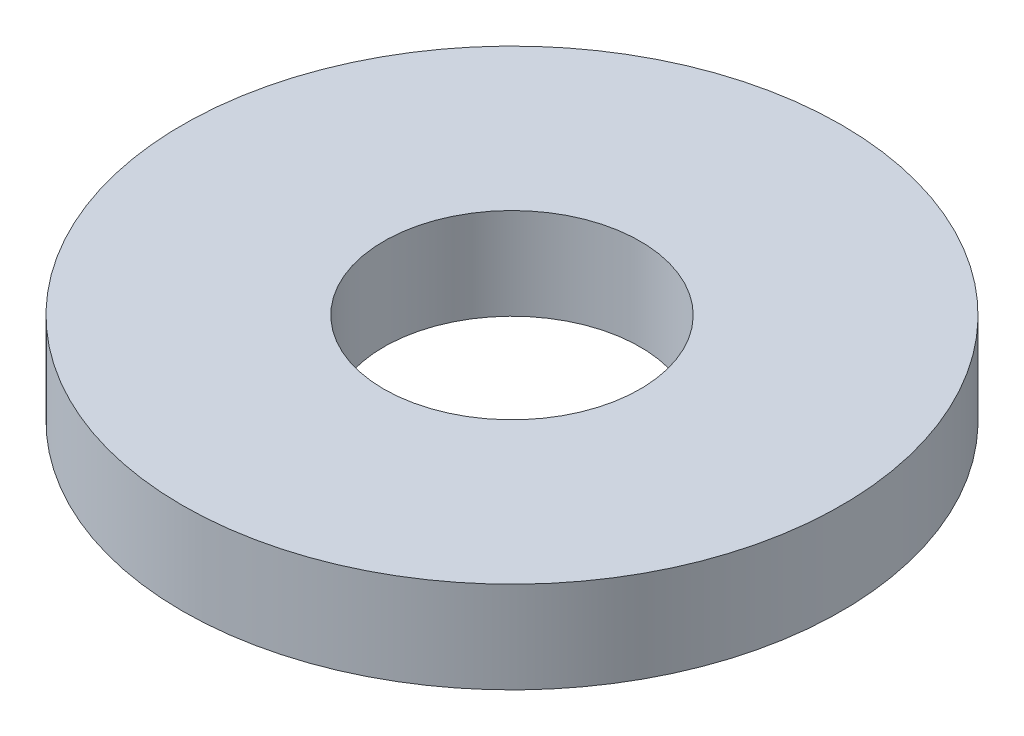
SolidWorks part; units mm, degrees
ref_plane "Front Plane" through (0, 0, 0) normal (0, 0, 1) x (1, 0, 0)
ref_plane "Top Plane" through (0, 0, 0) normal (0, 1, 0) x (1, 0, 0)
ref_plane "Right Plane" through (0, 0, 0) normal (1, 0, 0) x (0, 0, -1)
sketch "Sketch2" plane through (0, 0, 0) normal (0, 1, 0) x (1, 0, 0)
  circle A0 centre (0, 0) radius 3.5
  circle A1 centre (0, 0) radius 9
  dimension "D1" = 7
  dimension "D2" = 18
extrude "Boss-Extrude1" add sketch "Sketch2" along normal blind 2.5
